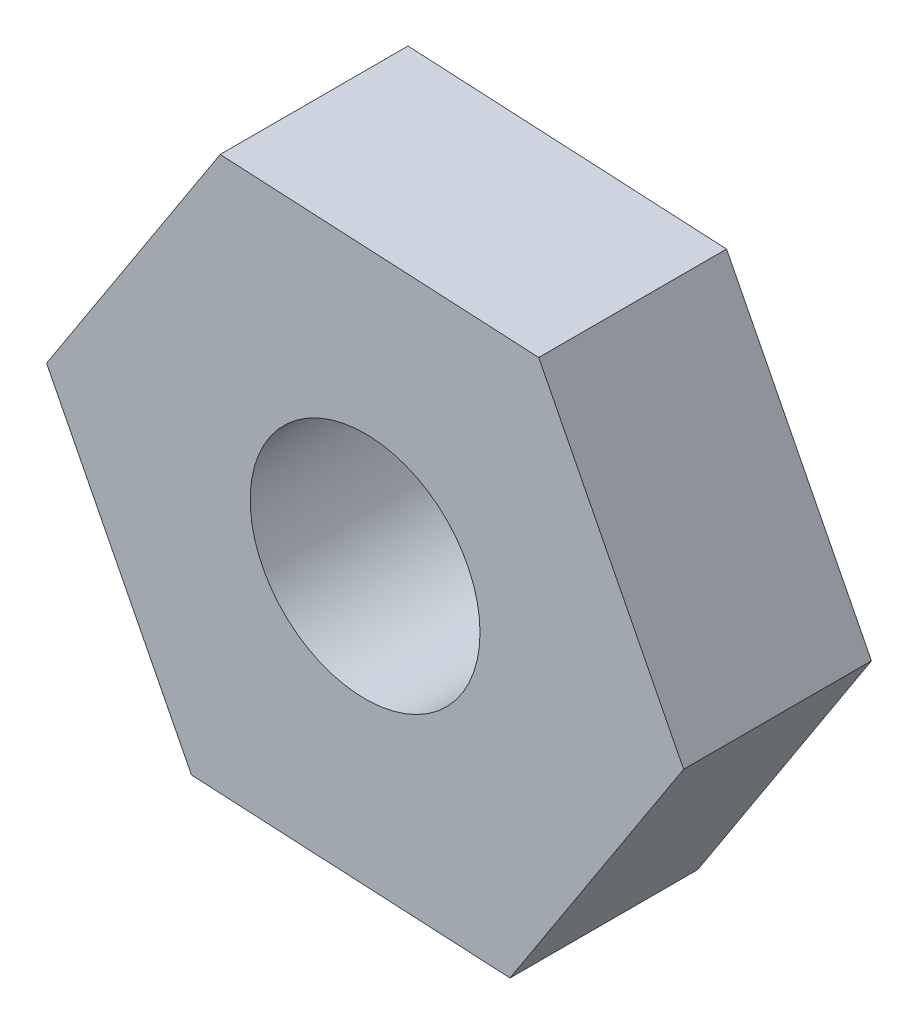
SolidWorks part; units mm, degrees
ref_plane "Front Plane" through (0, 0, 0) normal (0, 0, 1) x (1, 0, 0)
ref_plane "Top Plane" through (0, 0, 0) normal (0, 1, 0) x (1, 0, 0)
ref_plane "Right Plane" through (0, 0, 0) normal (1, 0, 0) x (0, 0, -1)
sketch "Sketch1" plane through (0, 0, 0) normal (0, 0, 1) x (1, 0, 0)
  line L1 (5.4011, -10.5911) -> (11.8727, -0.6181)
  line L2 (11.8727, -0.6181) -> (6.4717, 9.973)
  line L3 (6.4717, 9.973) -> (-5.4011, 10.5911)
  line L4 (-5.4011, 10.5911) -> (-11.8727, 0.6181)
  line L5 (-11.8727, 0.6181) -> (-6.4717, -9.973)
  line L6 (-6.4717, -9.973) -> (5.4011, -10.5911)
  circle A0 centre (0, 0) radius 10.296 construction
  circle A1 centre (0, 0) radius 4.2834
extrude "Boss-Extrude1" add sketch "Sketch1" along normal blind 7
